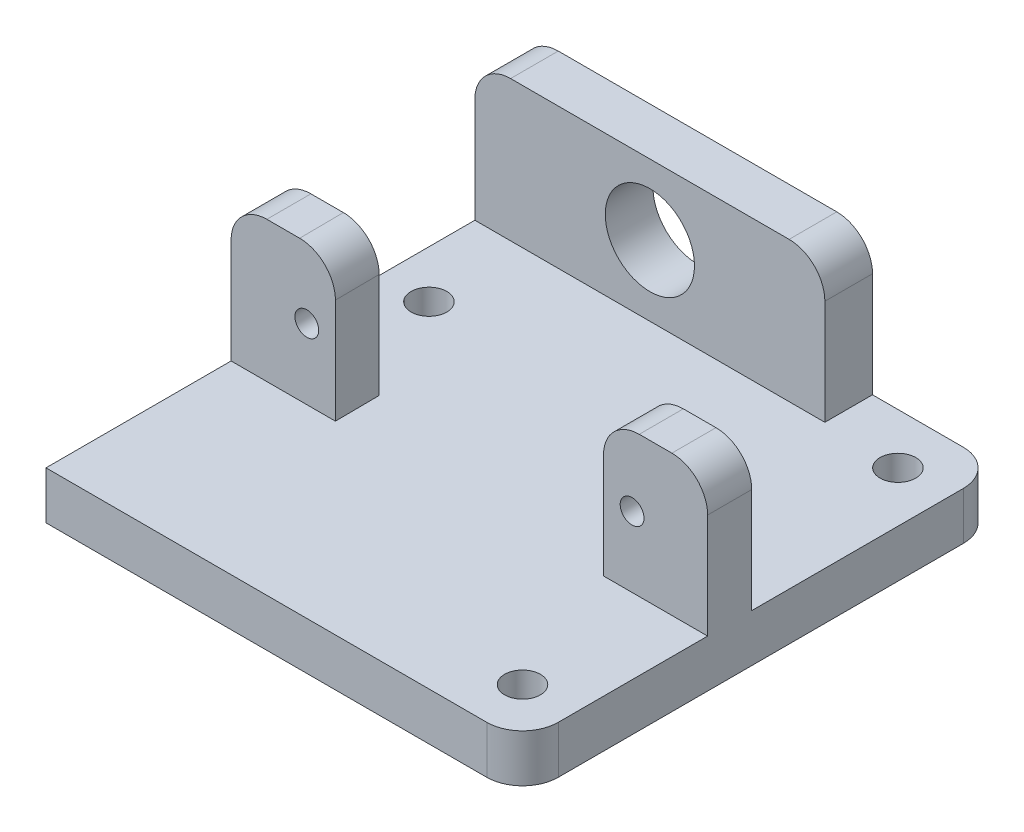
SolidWorks part; units mm, degrees
ref_plane "Front Plane" through (0, 0, 0) normal (0, 0, 1) x (1, 0, 0)
ref_plane "Top Plane" through (0, 0, 0) normal (0, 1, 0) x (1, 0, 0)
ref_plane "Right Plane" through (0, 0, 0) normal (1, 0, 0) x (0, 0, -1)
sketch "Sketch1" plane through (0, 0, 0) normal (0, 1, 0) x (1, 0, 0)
  line L1 (-20, -20) -> (20, -20)
  line L2 (-20, -20) -> (-20, 20)
  line L3 (-20, 20) -> (20, 20)
  line L4 (20, -20) -> (20, 20)
  line L5 (-20, -20) -> (20, 20) construction
  line L6 (-20, 20) -> (20, -20) construction
  point P0 (0, 0)
extrude "Boss-Extrude1" add sketch "Sketch1" along normal blind 4
ref_plane "Plane1" through (0, 4, 0) normal (0, 1, 0) x (1, 0, 0)
sketch "Sketch2" plane through (0, 4, 0) normal (0, 1, 0) x (1, 0, 0)
  line L0 (0, 29.8396) -> (0, -29.8396) construction
  line L1 (27.9528, 0) -> (-27.9528, 0) construction
  line L2 (11.2605, -0.7617) -> (11.2605, 3.2) construction
  line L3 (-20, -0.7617) -> (-11.2761, -0.7617)
  line L4 (0, -20) -> (0, -2.6117) construction
  line L5 (-20, -20) -> (20, -20) construction
  line L6 (-11.2605, -2.6117) -> (11.2605, -2.6117) construction
  line L7 (-20, -0.7617) -> (-20, -4.4617)
  line L8 (-20, -4.4617) -> (-11.2448, -4.4617)
  line L9 (-11.2761, -0.7617) -> (-11.2448, -4.4617)
  line L10 (-20, -0.7617) -> (-11.2448, -4.4617) construction
  line L11 (-20, -4.4617) -> (-11.2761, -0.7617) construction
  line L12 (11.2605, -0.7617) -> (20, -0.7617)
  line L13 (11.2605, -0.7617) -> (11.2605, -4.4617)
  line L14 (11.2605, -4.4617) -> (20, -4.4617)
  line L15 (20, -0.7617) -> (20, -4.4617)
  line L16 (11.2605, -0.7617) -> (20, -4.4617) construction
  line L17 (11.2605, -4.4617) -> (20, -0.7617) construction
  line L18 (-20, -4.4617) -> (-20, -4.4556) construction
  line L19 (-20, 20) -> (-20, -20) construction
  line L20 (20, -20) -> (20, 20) construction
  point P4 (0, 0)
  point P7 (0, 0)
  point P14 (0, -2.6117)
  point P24 (0, -2.6117)
  point P25 (0, -2.6117)
  dimension "D2" = 3.7
  dimension "D3" = 3.7
extrude "Boss-Extrude2" add sketch "Sketch2" along normal blind 11.8
sketch "Sketch3" plane through (0, 4, 0) normal (0, 1, 0) x (1, 0, 0)
  line L0 (9.38, 16) -> (-5.31, 16)
  line L1 (9.38, 16) -> (9.38, 20)
  line L2 (9.38, 20) -> (-5.31, 20)
  line L3 (-5.31, 20) -> (-20, 20)
  line L4 (-5.31, 20) -> (-5.31, 16) construction
  line L5 (-5.31, 16) -> (-20, 16)
  line L6 (-20, 20) -> (-20, 16)
  line L7 (20, 20) -> (-20, 20) construction
  line L8 (-20, 20) -> (-20, -0.7617) construction
extrude "Boss-Extrude3" add sketch "Sketch3" along normal blind 11.8
sketch "Sketch4" plane through (0, 0, -16) normal (0, 0, 1) x (1, 0, 0)
  line L2 (-20, 15.8) -> (-20, 4) construction
  line L3 (-20, 9.9) -> (-5.31, 9.9) construction
  circle A0 centre (-5.31, 9.9) radius 3.745
extrude "Cut-Extrude1" cut sketch "Sketch4" against normal through all
sketch "Sketch5" plane through (0, 0, 4.4617) normal (0, 0, 1) x (1, 0, 0)
  line L0 (-11.2448, 15.8) -> (-11.2448, 9.9) construction
  line L1 (-11.2448, 15.8) -> (-11.2448, 4) construction
  line L2 (-11.2448, 9.9) -> (-13.6448, 9.9) construction
  line L3 (11.2605, 15.8) -> (11.2605, 9.9) construction
  line L4 (11.2605, 15.8) -> (20, 15.8) construction
  line L5 (11.2605, 15.8) -> (11.2605, 4) construction
  line L6 (11.2605, 9.9) -> (13.6605, 9.9) construction
  circle A0 centre (-13.6448, 9.9) radius 1
  circle A1 centre (13.6605, 9.9) radius 1
extrude "Cut-Extrude2" cut sketch "Sketch5" against normal up to surface (3.7 mm away) up to face at (-15.638, 9.9, 0.7617)
sketch "Sketch6" plane through (0, 4, 0) normal (0, 1, 0) x (1, 0, 0)
  line L0 (20, 20) -> (15.7574, 15.7574) construction
  line L1 (20, -20) -> (15.7574, -15.7574) construction
  line L2 (-20, 8.1458) -> (-16, 8.1458)
  line L3 (-20, 16) -> (-20, -0.7617) construction
  circle A0 centre (15.7574, 15.7574) radius 1.5
  circle A1 centre (15.7574, -15.7574) radius 1.5
  circle A2 centre (-16, 8.1458) radius 1.5
extrude "Cut-Extrude3" cut sketch "Sketch6" against normal through all
fillet "Fillet1" radius 3 6 edges at (20, 15.8, 2.6117) (11.2605, 15.8, 2.6117) (9.38, 15.8, -18) (-20, 15.8, -18) (-20, 15.8, 2.6117) (-11.2605, 15.8, 2.6117)
fillet "Fillet2" radius 3 2 edges at (20, 2, -20) (20, 2, 20)
